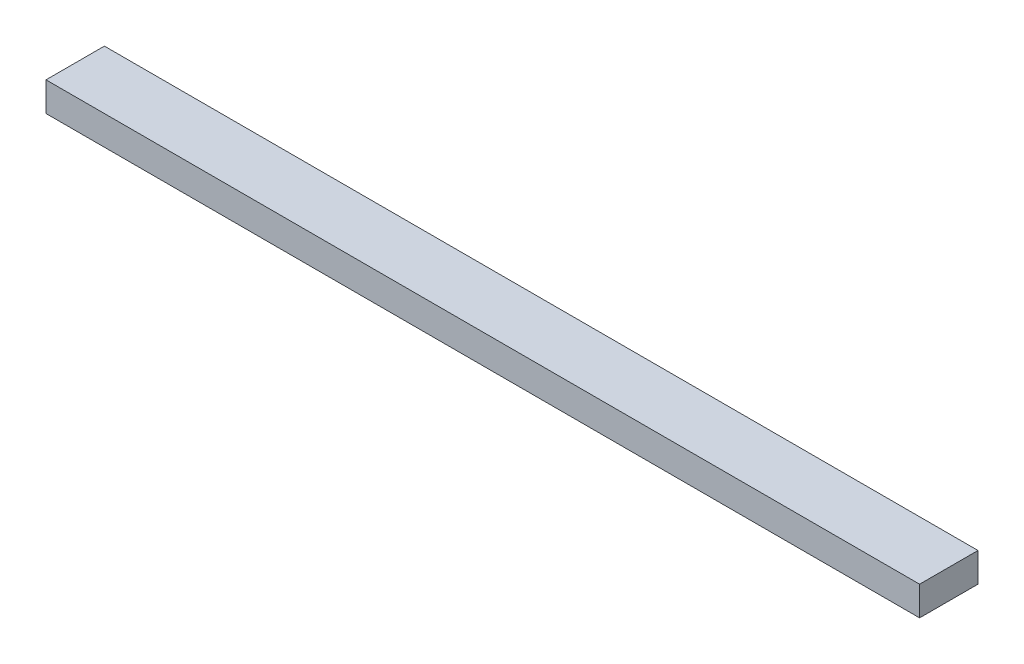
SolidWorks part; units mm, degrees
material "Pine"
ref_plane "Front Plane" through (0, 0, 0) normal (0, 0, 1) x (1, 0, 0)
ref_plane "Top Plane" through (0, 0, 0) normal (0, 1, 0) x (1, 0, 0)
ref_plane "Right Plane" through (0, 0, 0) normal (1, 0, 0) x (0, 0, -1)
sketch "Sketch1" plane through (0, 0, 0) normal (0, 1, 0) x (1, 0, 0)
  line L1 (0, 0) -> (569.9125, 0)
  line L2 (0, 0) -> (0, 38.1)
  line L3 (0, 38.1) -> (569.9125, 38.1)
  line L4 (569.9125, 0) -> (569.9125, 38.1)
  dimension "D1" = 38.1
  dimension "D2" = 569.9125
extrude "Boss-Extrude1" add sketch "Sketch1" along normal blind 19.05
